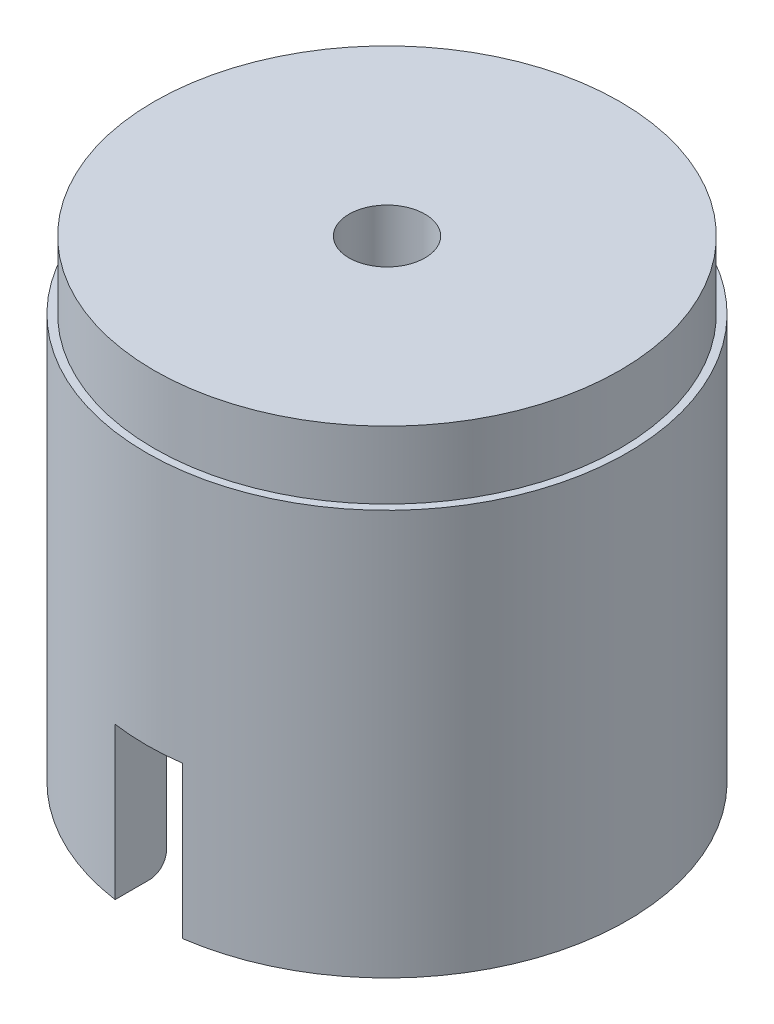
SolidWorks part; units mm, degrees
ref_plane "Front Plane" through (0, 0, 0) normal (0, 0, 1) x (1, 0, 0)
ref_plane "Top Plane" through (0, 0, 0) normal (0, 1, 0) x (1, 0, 0)
ref_plane "Right Plane" through (0, 0, 0) normal (1, 0, 0) x (0, 0, -1)
sketch "Sketch1" plane through (0, 0, 0) normal (0, 1, 0) x (1, 0, 0)
  circle A0 centre (0, 0) radius 11.25
  circle A1 centre (0, 0) radius 14.25
  dimension "D1" = 3
  dimension "D2" = 22.5
extrude "Boss-Extrude1" add sketch "Sketch1" along normal blind 24
sketch "Sketch2" plane through (0, 24, 0) normal (0, 1, 0) x (1, 0, 0)
  circle A0 centre (0, 0) radius 13.8
  circle A1 centre (0, 0) radius 2.25
  dimension "D1" = 4.5
extrude "Boss-Extrude2" add sketch "Sketch2" along normal blind 4
fillet "Fillet1" radius 1 1 edges at (0, 0, 11.25)
sketch "Sketch3" plane through (0, 0, 0) normal (0, -1, 0) x (1, 0, 0)
  line L0 (0, 14.25) -> (0, -14.25) construction
  line L1 (2, 14.25) -> (2, -14.25)
  line L2 (-2, 14.25) -> (-2, -14.25)
  arc A0 (2, 14.25) -> (-2, 14.25) centre (0, 14.25) ccw
  arc A1 (-2, -14.25) -> (2, -14.25) centre (0, -14.25) ccw
  circle A2 centre (0, 0) radius 14.25 construction
  point P2 (0, 0)
  dimension "D1" = 4
extrude "Cut-Extrude1" cut sketch "Sketch3" against normal offset from surface (9 mm away) 15 up to face at (0, 24, 11.25)
